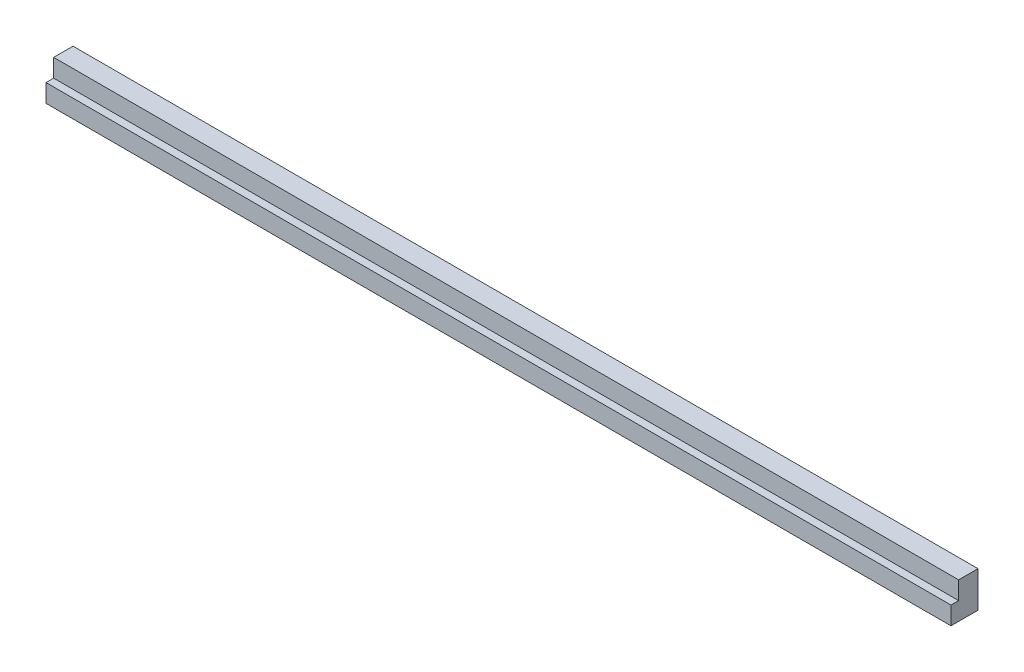
SolidWorks part; units mm, degrees
ref_plane "Plan de face" through (0, 0, 0) normal (0, 0, 1) x (1, 0, 0)
ref_plane "Plan de dessus" through (0, 0, 0) normal (0, 1, 0) x (1, 0, 0)
ref_plane "Plan de droite" through (0, 0, 0) normal (1, 0, 0) x (0, 0, -1)
sketch "Esquisse1" plane through (0, 0, 0) normal (0, 0, 1) x (1, 0, 0)
  line L0 (641, -201) -> (641, 261) construction
  line L1 (-364, -201) -> (641, -201)
  line L2 (-364, -201) -> (-364, -161)
  line L3 (-364, -161) -> (641, -161)
  line L4 (641, -201) -> (641, -161)
  dimension "D1" = 40
extrude "Boss.-Extru.1" add sketch "Esquisse1" along normal up to surface (21.5 mm away)
sketch "Esquisse2" plane through (0, 0, 21.5) normal (0, 0, 1) x (1, 0, 0)
  line L0 (-364, -201) -> (-364, -161) construction
  line L1 (641, -201) -> (-364, -201)
  line L2 (641, -201) -> (641, -181)
  line L3 (641, -181) -> (-364, -181)
  line L4 (-364, -201) -> (-364, -181)
extrude "Boss.-Extru.2" add sketch "Esquisse2" along normal up to surface (8.5 mm away)
